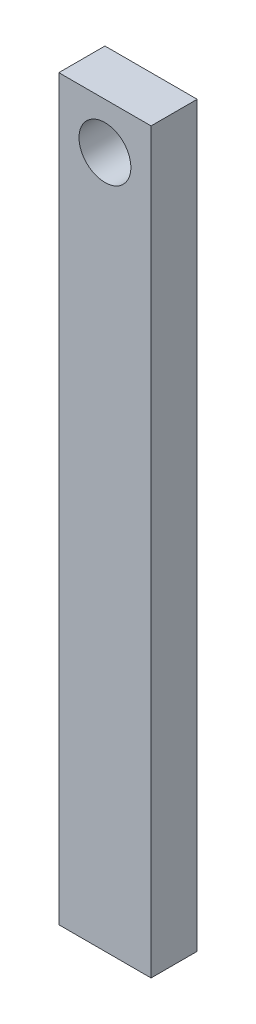
SolidWorks part; units mm, degrees
ref_plane "Front Plane" through (0, 0, 0) normal (0, 0, 1) x (1, 0, 0)
ref_plane "Top Plane" through (0, 0, 0) normal (0, 1, 0) x (1, 0, 0)
ref_plane "Right Plane" through (0, 0, 0) normal (1, 0, 0) x (0, 0, -1)
sketch "Sketch1" plane through (0, 0, 0) normal (0, 0, 1) x (1, 0, 0)
  line L1 (0, 0) -> (50.8, 0)
  line L2 (0, 0) -> (0, 406.4)
  line L3 (0, 406.4) -> (50.8, 406.4)
  line L4 (50.8, 0) -> (50.8, 406.4)
  circle A0 centre (25.4, 381) radius 14.2875
  point P8 (25.4, 406.4)
  dimension "D4" = 28.575
  dimension "D1" = 50.8
  dimension "D2" = 406.4
  dimension "D3" = 25.4
extrude "Boss-Extrude1" add sketch "Sketch1" along normal blind 25.4
